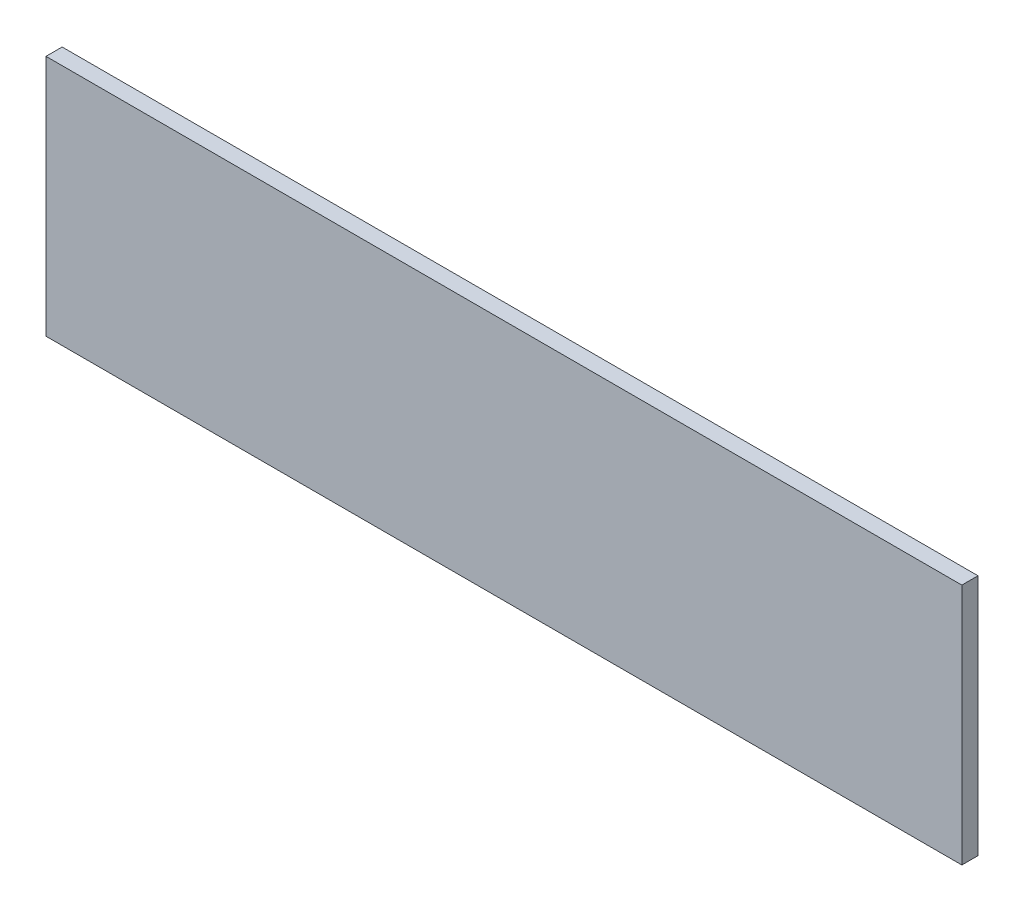
SolidWorks part; units mm, degrees
ref_plane "Alzado" through (0, 0, 0) normal (0, 0, 1) x (1, 0, 0)
ref_plane "Planta" through (0, 0, 0) normal (0, 1, 0) x (1, 0, 0)
ref_plane "Vista lateral" through (0, 0, 0) normal (1, 0, 0) x (0, 0, -1)
sketch "Croquis1" plane through (0, 0, 0) normal (0, 0, 1) x (1, 0, 0)
  line L1 (0, 0) -> (170, 0)
  line L2 (0, 0) -> (0, 45)
  line L3 (0, 45) -> (170, 45)
  line L4 (170, 0) -> (170, 45)
  dimension "D1" = 45
  dimension "D2" = 170
extrude "Saliente-Extruir1" add sketch "Croquis1" along normal blind 3
